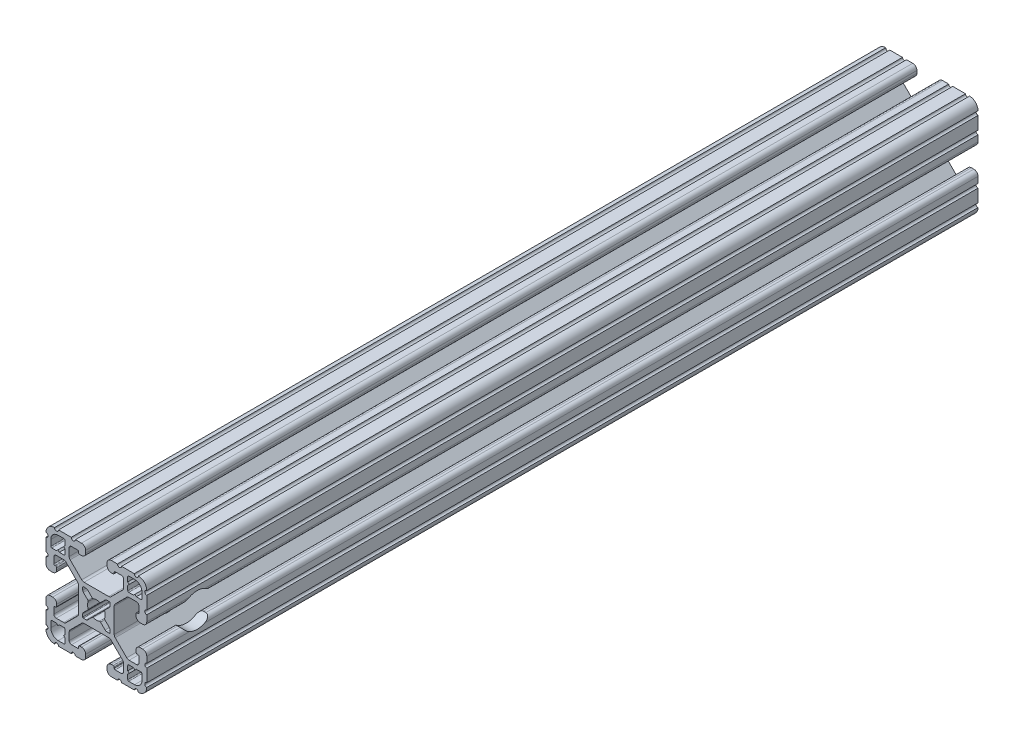
SolidWorks part; units mm, degrees
ref_plane "Front Plane" through (0, 0, 0) normal (0, 0, 1) x (1, 0, 0)
ref_plane "Top Plane" through (0, 0, 0) normal (0, 1, 0) x (1, 0, 0)
ref_plane "Right Plane" through (0, 0, 0) normal (1, 0, 0) x (0, 0, -1)
ref_plane "Plane1" through (0, 0, -2322.576) normal (0, 0, -1) x (-1, 0, 0)
sketch "Sketch1" plane through (0, 0, -2322.576) normal (0, 0, -1) x (-1, 0, 0)
  line L0 (17.2466, 14.4526) -> (17.2466, 12.2428)
  line L1 (16.8656, 11.8618) -> (15.0927, 11.8618)
  line L2 (15.0927, 11.8618) -> (14.5542, 12.4003)
  line L3 (14.5542, 12.4003) -> (14.0157, 11.8618)
  line L4 (14.0157, 11.8618) -> (12.2428, 11.8618)
  line L5 (11.8618, 12.2428) -> (11.8618, 14.0157)
  line L6 (11.8618, 14.0157) -> (12.4003, 14.5542)
  line L7 (12.4003, 14.5542) -> (11.8618, 15.0927)
  line L8 (11.8618, 15.0927) -> (11.8618, 16.8656)
  line L9 (12.2428, 17.2466) -> (14.4526, 17.2466)
  line L10 (17.2466, -12.2428) -> (17.2466, -14.4526)
  line L11 (14.4526, -17.2466) -> (12.2428, -17.2466)
  line L12 (11.8618, -16.8656) -> (11.8618, -15.0927)
  line L13 (11.8618, -15.0927) -> (12.4003, -14.5542)
  line L14 (12.4003, -14.5542) -> (11.8618, -14.0157)
  line L15 (11.8618, -14.0157) -> (11.8618, -12.2428)
  line L16 (12.2428, -11.8618) -> (14.0157, -11.8618)
  line L17 (14.0157, -11.8618) -> (14.5542, -12.4003)
  line L18 (14.5542, -12.4003) -> (15.0927, -11.8618)
  line L19 (15.0927, -11.8618) -> (16.8656, -11.8618)
  line L20 (5.1689, -3.9207) -> (5.1689, -4.9149)
  line L21 (4.9149, -5.1689) -> (3.9207, -5.1689)
  line L22 (3.2921, -4.9085) -> (1.5823, -3.1988)
  line L23 (-1.5823, -3.1988) -> (-3.2921, -4.9085)
  line L24 (-3.9207, -5.1689) -> (-4.9149, -5.1689)
  line L25 (-5.1689, -4.9149) -> (-5.1689, -3.9207)
  line L26 (-4.9085, -3.2921) -> (-3.1988, -1.5823)
  line L27 (-3.1988, 1.5823) -> (-4.9085, 3.2921)
  line L28 (-5.1689, 3.9207) -> (-5.1689, 4.9149)
  line L29 (-4.9149, 5.1689) -> (-3.9207, 5.1689)
  line L30 (-3.2921, 4.9085) -> (-1.5823, 3.1988)
  line L31 (1.5823, 3.1988) -> (3.2921, 4.9085)
  line L32 (3.9207, 5.1689) -> (4.9149, 5.1689)
  line L33 (5.1689, 4.9149) -> (5.1689, 3.9207)
  line L34 (4.9085, 3.2921) -> (3.1988, 1.5823)
  line L35 (3.1988, -1.5823) -> (4.9085, -3.2921)
  line L36 (-11.8618, -12.2428) -> (-11.8618, -14.0157)
  line L37 (-11.8618, -14.0157) -> (-12.4003, -14.5542)
  line L38 (-12.4003, -14.5542) -> (-11.8618, -15.0927)
  line L39 (-11.8618, -15.0927) -> (-11.8618, -16.8656)
  line L40 (-12.2428, -17.2466) -> (-14.4526, -17.2466)
  line L41 (-17.2466, -14.4526) -> (-17.2466, -12.2428)
  line L42 (-16.8656, -11.8618) -> (-15.0927, -11.8618)
  line L43 (-15.0927, -11.8618) -> (-14.5542, -12.4003)
  line L44 (-14.5542, -12.4003) -> (-14.0157, -11.8618)
  line L45 (-14.0157, -11.8618) -> (-12.2428, -11.8618)
  line L46 (-11.8618, 16.8656) -> (-11.8618, 15.0927)
  line L47 (-11.8618, 15.0927) -> (-12.4003, 14.5542)
  line L48 (-12.4003, 14.5542) -> (-11.8618, 14.0157)
  line L49 (-11.8618, 14.0157) -> (-11.8618, 12.2428)
  line L50 (-12.2428, 11.8618) -> (-14.0157, 11.8618)
  line L51 (-14.0157, 11.8618) -> (-14.5542, 12.4003)
  line L52 (-14.5542, 12.4003) -> (-15.0927, 11.8618)
  line L53 (-15.0927, 11.8618) -> (-16.8656, 11.8618)
  line L54 (-17.2466, 12.2428) -> (-17.2466, 14.4526)
  line L55 (-14.4526, 17.2466) -> (-12.2428, 17.2466)
  line L56 (19.05, -14.3256) -> (19.05, -9.4996)
  line L57 (19.05, -7.9756) -> (19.05, -5.6388)
  line L58 (17.4752, -4.064) -> (16.5608, -4.064)
  line L59 (14.986, -5.6388) -> (14.986, -6.35)
  line L60 (15.367, -6.731) -> (15.6972, -6.731)
  line L61 (16.0782, -7.112) -> (16.0782, -9.398)
  line L62 (15.1892, -10.287) -> (12.3756, -10.287)
  line L63 (11.4776, -9.915) -> (7.1157, -5.5531)
  line L64 (6.7437, -4.6551) -> (6.7437, 4.6551)
  line L65 (7.1157, 5.5531) -> (11.4776, 9.915)
  line L66 (12.3756, 10.287) -> (15.1892, 10.287)
  line L67 (16.0782, 9.398) -> (16.0782, 7.112)
  line L68 (15.6972, 6.731) -> (15.367, 6.731)
  line L69 (14.986, 6.35) -> (14.986, 5.6388)
  line L70 (16.5608, 4.064) -> (17.4752, 4.064)
  line L71 (19.05, 5.6388) -> (19.05, 7.9756)
  line L72 (19.05, 9.4996) -> (19.05, 14.3256)
  line L73 (14.3256, 19.05) -> (9.4996, 19.05)
  line L74 (7.9756, 19.05) -> (5.6388, 19.05)
  line L75 (4.064, 17.4752) -> (4.064, 16.5608)
  line L76 (5.6388, 14.986) -> (6.35, 14.986)
  line L77 (6.731, 15.367) -> (6.731, 15.6972)
  line L78 (7.112, 16.0782) -> (9.398, 16.0782)
  line L79 (10.287, 15.1892) -> (10.287, 12.3756)
  line L80 (9.915, 11.4776) -> (5.5531, 7.1157)
  line L81 (4.6551, 6.7437) -> (-4.6551, 6.7437)
  line L82 (-5.5531, 7.1157) -> (-9.915, 11.4776)
  line L83 (-10.287, 12.3756) -> (-10.287, 15.1892)
  line L84 (-9.398, 16.0782) -> (-7.112, 16.0782)
  line L85 (-6.731, 15.6972) -> (-6.731, 15.367)
  line L86 (-6.35, 14.986) -> (-5.6388, 14.986)
  line L87 (-4.064, 16.5608) -> (-4.064, 17.4752)
  line L88 (-5.6388, 19.05) -> (-7.9756, 19.05)
  line L89 (-9.4996, 19.05) -> (-14.3256, 19.05)
  line L90 (-19.05, 14.3256) -> (-19.05, 9.4996)
  line L91 (-19.05, 7.9756) -> (-19.05, 5.6388)
  line L92 (-17.4752, 4.064) -> (-16.5608, 4.064)
  line L93 (-14.986, 5.6388) -> (-14.986, 6.35)
  line L94 (-15.367, 6.731) -> (-15.6972, 6.731)
  line L95 (-16.0782, 7.112) -> (-16.0782, 9.398)
  line L96 (-15.1892, 10.287) -> (-12.3756, 10.287)
  line L97 (-11.4776, 9.915) -> (-7.1157, 5.5531)
  line L98 (-6.7437, 4.6551) -> (-6.7437, -4.6551)
  line L99 (-7.1157, -5.5531) -> (-11.4776, -9.915)
  line L100 (-12.3756, -10.287) -> (-15.1892, -10.287)
  line L101 (-16.0782, -9.398) -> (-16.0782, -7.112)
  line L102 (-15.6972, -6.731) -> (-15.367, -6.731)
  line L103 (-14.986, -6.35) -> (-14.986, -5.6388)
  line L104 (-16.5608, -4.064) -> (-17.4752, -4.064)
  line L105 (-19.05, -5.6388) -> (-19.05, -7.9756)
  line L106 (-19.05, -9.4996) -> (-19.05, -14.3256)
  line L107 (-14.3256, -19.05) -> (-9.4996, -19.05)
  line L108 (-7.9756, -19.05) -> (-5.6388, -19.05)
  line L109 (-4.064, -17.4752) -> (-4.064, -16.5608)
  line L110 (-5.6388, -14.986) -> (-6.35, -14.986)
  line L111 (-6.731, -15.367) -> (-6.731, -15.6972)
  line L112 (-7.112, -16.0782) -> (-9.398, -16.0782)
  line L113 (-10.287, -15.1892) -> (-10.287, -12.3756)
  line L114 (-9.915, -11.4776) -> (-5.5531, -7.1157)
  line L115 (-4.6551, -6.7437) -> (4.6551, -6.7437)
  line L116 (5.5531, -7.1157) -> (9.915, -11.4776)
  line L117 (10.287, -12.3756) -> (10.287, -15.1892)
  line L118 (9.398, -16.0782) -> (7.112, -16.0782)
  line L119 (6.731, -15.6972) -> (6.731, -15.367)
  line L120 (6.35, -14.986) -> (5.6388, -14.986)
  line L121 (4.064, -16.5608) -> (4.064, -17.4752)
  line L122 (5.6388, -19.05) -> (7.9756, -19.05)
  line L123 (9.4996, -19.05) -> (14.3256, -19.05)
  arc A0 (17.2466, 12.2428) -> (16.8656, 11.8618) centre (16.8656, 12.2428) cw
  arc A1 (12.2428, 11.8618) -> (11.8618, 12.2428) centre (12.2428, 12.2428) cw
  arc A2 (11.8618, 16.8656) -> (12.2428, 17.2466) centre (12.2428, 16.8656) cw
  arc A3 (14.4526, 17.2466) -> (17.2466, 14.4526) centre (14.4526, 14.4526) cw
  arc A4 (17.2466, -14.4526) -> (14.4526, -17.2466) centre (14.4526, -14.4526) cw
  arc A5 (12.2428, -17.2466) -> (11.8618, -16.8656) centre (12.2428, -16.8656) cw
  arc A6 (11.8618, -12.2428) -> (12.2428, -11.8618) centre (12.2428, -12.2428) cw
  arc A7 (16.8656, -11.8618) -> (17.2466, -12.2428) centre (16.8656, -12.2428) cw
  arc A8 (5.1689, -4.9149) -> (4.9149, -5.1689) centre (4.9149, -4.9149) cw
  arc A9 (3.9207, -5.1689) -> (3.2921, -4.9085) centre (3.9207, -4.2799) cw
  arc A10 (1.5823, -3.1988) -> (1.178, -3.1119) centre (1.3129, -3.4682) ccw
  arc A11 (1.178, -3.1119) -> (-1.178, -3.1119) centre (0, 0) cw
  arc A12 (-1.178, -3.1119) -> (-1.5823, -3.1988) centre (-1.3129, -3.4682) ccw
  arc A13 (-3.2921, -4.9085) -> (-3.9207, -5.1689) centre (-3.9207, -4.2799) cw
  arc A14 (-4.9149, -5.1689) -> (-5.1689, -4.9149) centre (-4.9149, -4.9149) cw
  arc A15 (-5.1689, -3.9207) -> (-4.9085, -3.2921) centre (-4.2799, -3.9207) cw
  arc A16 (-3.1988, -1.5823) -> (-3.1119, -1.178) centre (-3.4682, -1.3129) ccw
  arc A17 (-3.1119, -1.178) -> (-3.1119, 1.178) centre (0, 0) cw
  arc A18 (-3.1119, 1.178) -> (-3.1988, 1.5823) centre (-3.4682, 1.3129) ccw
  arc A19 (-4.9085, 3.2921) -> (-5.1689, 3.9207) centre (-4.2799, 3.9207) cw
  arc A20 (-5.1689, 4.9149) -> (-4.9149, 5.1689) centre (-4.9149, 4.9149) cw
  arc A21 (-3.9207, 5.1689) -> (-3.2921, 4.9085) centre (-3.9207, 4.2799) cw
  arc A22 (-1.5823, 3.1988) -> (-1.178, 3.1119) centre (-1.3129, 3.4682) ccw
  arc A23 (-1.178, 3.1119) -> (1.178, 3.1119) centre (0, 0) cw
  arc A24 (1.178, 3.1119) -> (1.5823, 3.1988) centre (1.3129, 3.4682) ccw
  arc A25 (3.2921, 4.9085) -> (3.9207, 5.1689) centre (3.9207, 4.2799) cw
  arc A26 (4.9149, 5.1689) -> (5.1689, 4.9149) centre (4.9149, 4.9149) cw
  arc A27 (5.1689, 3.9207) -> (4.9085, 3.2921) centre (4.2799, 3.9207) cw
  arc A28 (3.1988, 1.5823) -> (3.1119, 1.178) centre (3.4682, 1.3129) ccw
  arc A29 (3.1119, 1.178) -> (3.1119, -1.178) centre (0, 0) cw
  arc A30 (3.1119, -1.178) -> (3.1988, -1.5823) centre (3.4682, -1.3129) ccw
  arc A31 (4.9085, -3.2921) -> (5.1689, -3.9207) centre (4.2799, -3.9207) cw
  arc A32 (-11.8618, -16.8656) -> (-12.2428, -17.2466) centre (-12.2428, -16.8656) cw
  arc A33 (-14.4526, -17.2466) -> (-17.2466, -14.4526) centre (-14.4526, -14.4526) cw
  arc A34 (-17.2466, -12.2428) -> (-16.8656, -11.8618) centre (-16.8656, -12.2428) cw
  arc A35 (-12.2428, -11.8618) -> (-11.8618, -12.2428) centre (-12.2428, -12.2428) cw
  arc A36 (-12.2428, 17.2466) -> (-11.8618, 16.8656) centre (-12.2428, 16.8656) cw
  arc A37 (-11.8618, 12.2428) -> (-12.2428, 11.8618) centre (-12.2428, 12.2428) cw
  arc A38 (-16.8656, 11.8618) -> (-17.2466, 12.2428) centre (-16.8656, 12.2428) cw
  arc A39 (-17.2466, 14.4526) -> (-14.4526, 17.2466) centre (-14.4526, 14.4526) cw
  arc A40 (19.05, -9.4996) -> (19.05, -7.9756) centre (19.05, -8.7376) cw
  arc A41 (19.05, -5.6388) -> (17.4752, -4.064) centre (17.4752, -5.6388) ccw
  arc A42 (16.5608, -4.064) -> (14.986, -5.6388) centre (16.5608, -5.6388) ccw
  arc A43 (14.986, -6.35) -> (15.367, -6.731) centre (15.367, -6.35) ccw
  arc A44 (15.6972, -6.731) -> (16.0782, -7.112) centre (15.6972, -7.112) cw
  arc A45 (16.0782, -9.398) -> (15.1892, -10.287) centre (15.1892, -9.398) cw
  arc A46 (12.3756, -10.287) -> (11.4776, -9.915) centre (12.3756, -9.017) cw
  arc A47 (7.1157, -5.5531) -> (6.7437, -4.6551) centre (8.0137, -4.6551) cw
  arc A48 (6.7437, 4.6551) -> (7.1157, 5.5531) centre (8.0137, 4.6551) cw
  arc A49 (11.4776, 9.915) -> (12.3756, 10.287) centre (12.3756, 9.017) cw
  arc A50 (15.1892, 10.287) -> (16.0782, 9.398) centre (15.1892, 9.398) cw
  arc A51 (16.0782, 7.112) -> (15.6972, 6.731) centre (15.6972, 7.112) cw
  arc A52 (15.367, 6.731) -> (14.986, 6.35) centre (15.367, 6.35) ccw
  arc A53 (14.986, 5.6388) -> (16.5608, 4.064) centre (16.5608, 5.6388) ccw
  arc A54 (17.4752, 4.064) -> (19.05, 5.6388) centre (17.4752, 5.6388) ccw
  arc A55 (19.05, 7.9756) -> (19.05, 9.4996) centre (19.05, 8.7376) cw
  arc A56 (19.05, 14.3256) -> (19.0499, 15.8496) centre (19.05, 15.0876) cw
  arc A57 (19.0499, 15.8496) -> (15.8496, 19.0499) centre (15.875, 15.875) ccw
  arc A58 (15.8496, 19.0499) -> (14.3256, 19.05) centre (15.0876, 19.05) cw
  arc A59 (9.4996, 19.05) -> (7.9756, 19.05) centre (8.7376, 19.05) cw
  arc A60 (5.6388, 19.05) -> (4.064, 17.4752) centre (5.6388, 17.4752) ccw
  arc A61 (4.064, 16.5608) -> (5.6388, 14.986) centre (5.6388, 16.5608) ccw
  arc A62 (6.35, 14.986) -> (6.731, 15.367) centre (6.35, 15.367) ccw
  arc A63 (6.731, 15.6972) -> (7.112, 16.0782) centre (7.112, 15.6972) cw
  arc A64 (9.398, 16.0782) -> (10.287, 15.1892) centre (9.398, 15.1892) cw
  arc A65 (10.287, 12.3756) -> (9.915, 11.4776) centre (9.017, 12.3756) cw
  arc A66 (5.5531, 7.1157) -> (4.6551, 6.7437) centre (4.6551, 8.0137) cw
  arc A67 (-4.6551, 6.7437) -> (-5.5531, 7.1157) centre (-4.6551, 8.0137) cw
  arc A68 (-9.915, 11.4776) -> (-10.287, 12.3756) centre (-9.017, 12.3756) cw
  arc A69 (-10.287, 15.1892) -> (-9.398, 16.0782) centre (-9.398, 15.1892) cw
  arc A70 (-7.112, 16.0782) -> (-6.731, 15.6972) centre (-7.112, 15.6972) cw
  arc A71 (-6.731, 15.367) -> (-6.35, 14.986) centre (-6.35, 15.367) ccw
  arc A72 (-5.6388, 14.986) -> (-4.064, 16.5608) centre (-5.6388, 16.5608) ccw
  arc A73 (-4.064, 17.4752) -> (-5.6388, 19.05) centre (-5.6388, 17.4752) ccw
  arc A74 (-7.9756, 19.05) -> (-9.4996, 19.05) centre (-8.7376, 19.05) cw
  arc A75 (-14.3256, 19.05) -> (-15.8496, 19.0499) centre (-15.0876, 19.05) cw
  arc A76 (-15.8496, 19.0499) -> (-19.0499, 15.8496) centre (-15.875, 15.875) ccw
  arc A77 (-19.0499, 15.8496) -> (-19.05, 14.3256) centre (-19.05, 15.0876) cw
  arc A78 (-19.05, 9.4996) -> (-19.05, 7.9756) centre (-19.05, 8.7376) cw
  arc A79 (-19.05, 5.6388) -> (-17.4752, 4.064) centre (-17.4752, 5.6388) ccw
  arc A80 (-16.5608, 4.064) -> (-14.986, 5.6388) centre (-16.5608, 5.6388) ccw
  arc A81 (-14.986, 6.35) -> (-15.367, 6.731) centre (-15.367, 6.35) ccw
  arc A82 (-15.6972, 6.731) -> (-16.0782, 7.112) centre (-15.6972, 7.112) cw
  arc A83 (-16.0782, 9.398) -> (-15.1892, 10.287) centre (-15.1892, 9.398) cw
  arc A84 (-12.3756, 10.287) -> (-11.4776, 9.915) centre (-12.3756, 9.017) cw
  arc A85 (-7.1157, 5.5531) -> (-6.7437, 4.6551) centre (-8.0137, 4.6551) cw
  arc A86 (-6.7437, -4.6551) -> (-7.1157, -5.5531) centre (-8.0137, -4.6551) cw
  arc A87 (-11.4776, -9.915) -> (-12.3756, -10.287) centre (-12.3756, -9.017) cw
  arc A88 (-15.1892, -10.287) -> (-16.0782, -9.398) centre (-15.1892, -9.398) cw
  arc A89 (-16.0782, -7.112) -> (-15.6972, -6.731) centre (-15.6972, -7.112) cw
  arc A90 (-15.367, -6.731) -> (-14.986, -6.35) centre (-15.367, -6.35) ccw
  arc A91 (-14.986, -5.6388) -> (-16.5608, -4.064) centre (-16.5608, -5.6388) ccw
  arc A92 (-17.4752, -4.064) -> (-19.05, -5.6388) centre (-17.4752, -5.6388) ccw
  arc A93 (-19.05, -7.9756) -> (-19.05, -9.4996) centre (-19.05, -8.7376) cw
  arc A94 (-19.05, -14.3256) -> (-19.0499, -15.8496) centre (-19.05, -15.0876) cw
  arc A95 (-19.0499, -15.8496) -> (-15.8496, -19.0499) centre (-15.875, -15.875) ccw
  arc A96 (-15.8496, -19.0499) -> (-14.3256, -19.05) centre (-15.0876, -19.05) cw
  arc A97 (-9.4996, -19.05) -> (-7.9756, -19.05) centre (-8.7376, -19.05) cw
  arc A98 (-5.6388, -19.05) -> (-4.064, -17.4752) centre (-5.6388, -17.4752) ccw
  arc A99 (-4.064, -16.5608) -> (-5.6388, -14.986) centre (-5.6388, -16.5608) ccw
  arc A100 (-6.35, -14.986) -> (-6.731, -15.367) centre (-6.35, -15.367) ccw
  arc A101 (-6.731, -15.6972) -> (-7.112, -16.0782) centre (-7.112, -15.6972) cw
  arc A102 (-9.398, -16.0782) -> (-10.287, -15.1892) centre (-9.398, -15.1892) cw
  arc A103 (-10.287, -12.3756) -> (-9.915, -11.4776) centre (-9.017, -12.3756) cw
  arc A104 (-5.5531, -7.1157) -> (-4.6551, -6.7437) centre (-4.6551, -8.0137) cw
  arc A105 (4.6551, -6.7437) -> (5.5531, -7.1157) centre (4.6551, -8.0137) cw
  arc A106 (9.915, -11.4776) -> (10.287, -12.3756) centre (9.017, -12.3756) cw
  arc A107 (10.287, -15.1892) -> (9.398, -16.0782) centre (9.398, -15.1892) cw
  arc A108 (7.112, -16.0782) -> (6.731, -15.6972) centre (7.112, -15.6972) cw
  arc A109 (6.731, -15.367) -> (6.35, -14.986) centre (6.35, -15.367) ccw
  arc A110 (5.6388, -14.986) -> (4.064, -16.5608) centre (5.6388, -16.5608) ccw
  arc A111 (4.064, -17.4752) -> (5.6388, -19.05) centre (5.6388, -17.4752) ccw
  arc A112 (7.9756, -19.05) -> (9.4996, -19.05) centre (8.7376, -19.05) cw
  arc A113 (14.3256, -19.05) -> (15.8496, -19.0499) centre (15.0876, -19.05) cw
  arc A114 (15.8496, -19.0499) -> (19.0499, -15.8496) centre (15.875, -15.875) ccw
  arc A115 (19.0499, -15.8496) -> (19.05, -14.3256) centre (19.05, -15.0876) cw
extrude "Boss-Extrude1" add sketch "Sketch1" against normal blind 314.325
sketch "Sketch2" plane through (19.05, 0, 0) normal (1, 0, 0) x (0, 0, -1)
  line L0 (2008.251, 4.6551) -> (2008.251, -4.6551) construction
  circle A0 centre (2027.301, 0) radius 6.35
  dimension "D1" = 19.05
extrude "Cut-Extrude1" cut sketch "Sketch2" against normal through all
